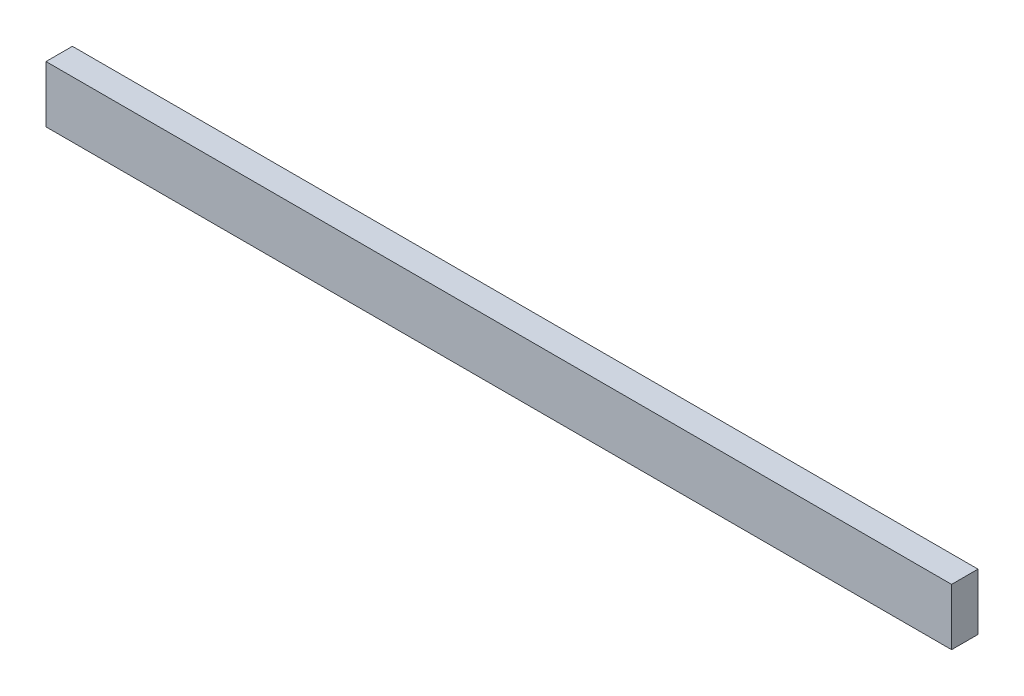
SolidWorks part; units mm, degrees
ref_plane "Front Plane" through (0, 0, 0) normal (0, 0, 1) x (1, 0, 0)
ref_plane "Top Plane" through (0, 0, 0) normal (0, 1, 0) x (1, 0, 0)
ref_plane "Right Plane" through (0, 0, 0) normal (1, 0, 0) x (0, 0, -1)
sketch "Sketch1" plane through (0, 0, 0) normal (0, 0, 1) x (1, 0, 0)
  line L1 (-65.3526, 22.3864) -> (544.2474, 22.3864)
  line L2 (-65.3526, 22.3864) -> (-65.3526, -15.7136)
  line L3 (-65.3526, -15.7136) -> (544.2474, -15.7136)
  line L4 (544.2474, 22.3864) -> (544.2474, -15.7136)
  dimension "D1" = 609.6
  dimension "D2" = 38.1
extrude "Boss-Extrude1" add sketch "Sketch1" along normal blind 17.78
